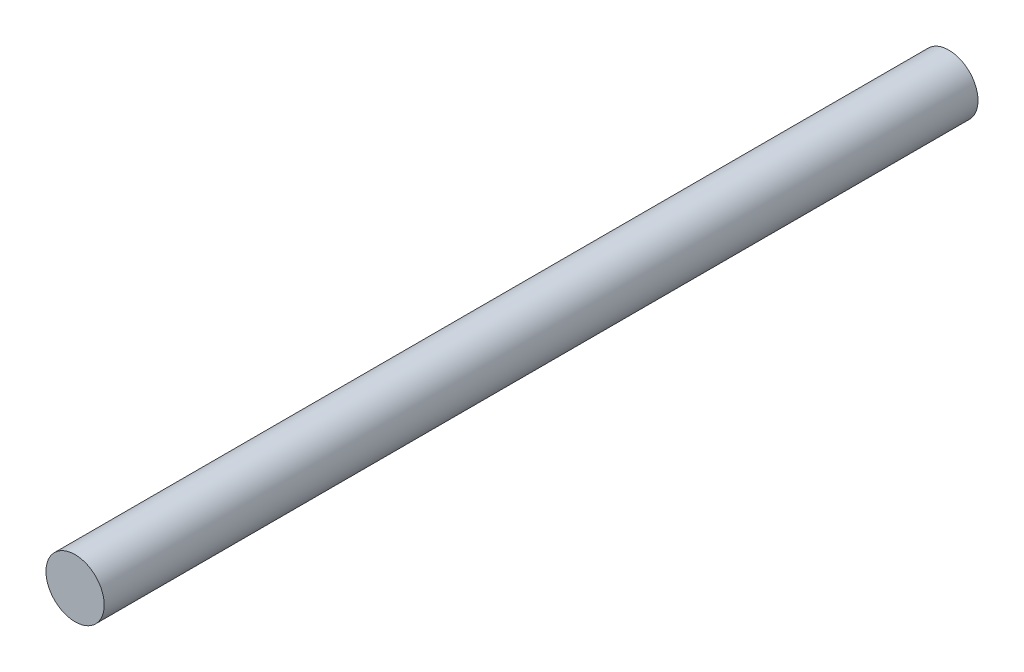
SolidWorks part; units mm, degrees
ref_plane "Front Plane" through (0, 0, 0) normal (0, 0, 1) x (1, 0, 0)
ref_plane "Top Plane" through (0, 0, 0) normal (0, 1, 0) x (1, 0, 0)
ref_plane "Right Plane" through (0, 0, 0) normal (1, 0, 0) x (0, 0, -1)
sketch "Sketch1" plane through (0, 0, 0) normal (0, 0, 1) x (1, 0, 0)
  circle A0 centre (0, 0) radius 50
  dimension "D1" = 100
extrude "Boss-Extrude1" add sketch "Sketch1" along normal mid plane 1500
